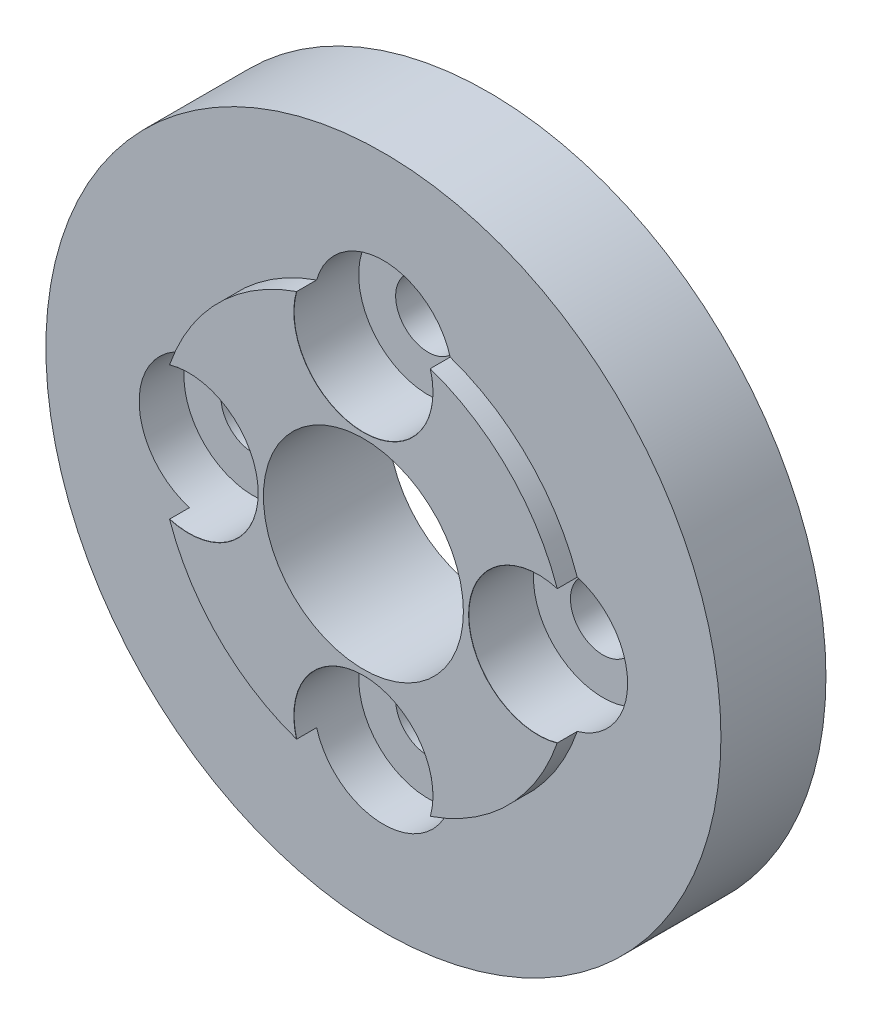
SolidWorks part; units mm, degrees
material "Aleación 6061"
ref_plane "Alzado" through (0, 0, 0) normal (0, 0, 1) x (1, 0, 0)
ref_plane "Planta" through (0, 0, 0) normal (0, 1, 0) x (1, 0, 0)
ref_plane "Vista lateral" through (0, 0, 0) normal (1, 0, 0) x (0, 0, -1)
sketch "Croquis1" plane through (0, 0, 0) normal (0, 0, 1) x (1, 0, 0)
  circle A0 centre (0, 0) radius 67.5
  circle A1 centre (0, 0) radius 20
  dimension "D1" = 40
  dimension "D2" = 135
extrude "Saliente-Extruir1" add sketch "Croquis1" along normal blind 21
sketch "Croquis2" plane through (0, 0, 21) normal (0, 0, 1) x (1, 0, 0)
  circle A0 centre (0, 0) radius 41
  circle A1 centre (0, 0) radius 20 construction
  circle A2 centre (0, 0) radius 20
  dimension "D1" = 82
extrude "Saliente-Extruir2" add sketch "Croquis2" along normal blind 4
sketch "Croquis3" plane through (0, 0, 25) normal (0, 0, 1) x (1, 0, 0)
  line L0 (0, 0) -> (0, 34.95) construction
  dimension "D1" = 34.95
sketch "Croquis8" plane through (0, 0, 0) normal (0, 0, 1) x (1, 0, 0)
  line L0 (0, 0) -> (0, 50000) construction
  line L5 (-12.5, 15.6125) -> (-12.5, 16.4317)
  line L6 (12.5, 15.6125) -> (12.5, 16.4317)
  arc A0 (-12.5, 15.6125) -> (12.5, 15.6125) centre (0, 0) cw
  circle A1 centre (0, 0) radius 20 construction
  arc A2 (-9.4231, 14.7464) -> (9.4231, 14.7464) centre (0, 0) cw
  arc A3 (12.5, 16.4317) -> (9.4231, 14.7464) centre (10.5, 16.4317) cw
  arc A4 (-12.5, 16.4317) -> (-9.4231, 14.7464) centre (-10.5, 16.4317) ccw
  point P8 (10.8312, 13.2752)
  point P11 (0, 0.5545)
  point P12 (0, 0)
  point P16 (12.5, 12.2474)
  point P19 (-12.5, 12.2474)
  dimension "D1" = 17.5
  dimension "D3" = 2
  dimension "D2" = 25
extrude "Saliente-Extruir3" [suppressed] add sketch "Croquis8" along normal up to surface (25 mm away)
pattern_circular "MatrizC2" [suppressed] count 4 every 90
hole_wizard "Refrentado para perno con cabeza hexagonal de M122" positions "Croquis6" profile "Croquis7" counterbore size "M12" standard "Ansi Metric" end condition through all
sketch "Croquis6" plane through (0, 0, 25) normal (0, 0, 1) x (1, 0, 0)
  point P0 (0, 34.95)
sketch "Croquis7" plane through (0, 34.95, 25) normal (1, 0, 0) x (0, -1, 0)
  line L0 (0, 0) -> (0, 25)
  line L1 (0, 25) -> (6.5, 25)
  line L3 (6.5, 25) -> (6.5, 12.95)
  line L4 (13.89, 12.95) -> (6.5, 12.95)
  line L5 (13.89, 12.95) -> (13.89, 0.025)
  line L6 (13.89, 0.025) -> (13.915, 0)
  line L7 (13.915, 0) -> (0, 0)
  line L8 (-13.89, 0.025) -> (-13.915, 0) construction
  line L11 (0, -6.35) -> (0, 107.95) construction
  dimension "Diámetro de taladro hasta el siguiente" = 13
  dimension "Profundidad de taladro hasta el siguiente" = 25
  dimension "Diámetro de refrentado" = 27.78
  dimension "Profundidad de refrentado" = 12.95
  dimension "Diámetro de avellanado cercano" = 27.83
  dimension "Ángulo de avellanado cercano" = 90
pattern_circular "MatrizC1" count 4 every 90 about axis through (0, 0, 0) along (0, 0, 1) of "Refrentado para perno con cabeza hexagonal de M122"
